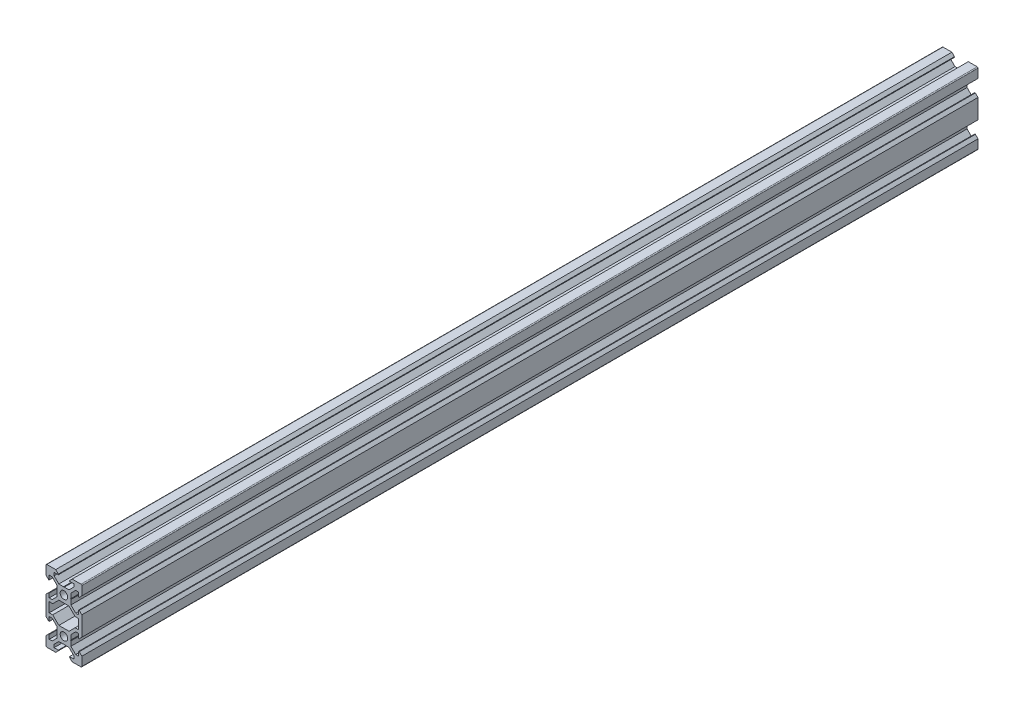
SolidWorks part; units mm, degrees
ref_plane "Front Plane" through (0, 0, 0) normal (0, 0, 1) x (1, 0, 0)
ref_plane "Top Plane" through (0, 0, 0) normal (0, 1, 0) x (1, 0, 0)
ref_plane "Right Plane" through (0, 0, 0) normal (1, 0, 0) x (0, 0, -1)
sketch "Sketch1" plane through (0, 0, 0) normal (0, 0, 1) x (1, 0, 0)
  line B0 (-8.2, -12.7) -> (-6.2393, -12.7)
  line B1 (-6.2393, -12.7) -> (-2.8393, -16.1)
  line B2 (-2.8393, -16.1) -> (2.8393, -16.1)
  line B3 (6.2393, -12.7) -> (2.8393, -16.1)
  line B4 (8.2, -12.7) -> (6.2393, -12.7)
  line B5 (8.2, -12.7) -> (8.2, -7.3)
  line B6 (8.2, -7.3) -> (6.2393, -7.3)
  line B7 (6.2393, -7.3) -> (2.8393, -3.9)
  line B8 (-2.8393, -3.9) -> (2.8393, -3.9)
  line B9 (-6.2393, -7.3) -> (-2.8393, -3.9)
  line B10 (-8.2, -7.3) -> (-6.2393, -7.3)
  line B11 (-8.2, -12.7) -> (-8.2, -7.3)
  line B12 (3.69, 0) -> (3.9, -0.21)
  line B13 (3.9, -0.21) -> (3.9, -2.8393)
  line B14 (3.9, -2.8393) -> (6.5607, -5.5)
  line B15 (6.5607, -5.5) -> (8.2, -5.5)
  line B16 (8.2, -5.5) -> (8.2, -3.125)
  line B17 (8.2, -3.125) -> (8.545, -3.125)
  line B18 (8.545, -3.125) -> (10, -4.58)
  line B19 (10, -15.42) -> (10, -4.58)
  line B20 (8.545, -16.875) -> (10, -15.42)
  line B21 (8.2, -16.875) -> (8.545, -16.875)
  line B22 (8.2, -14.5) -> (8.2, -16.875)
  line B23 (6.5607, -14.5) -> (8.2, -14.5)
  line B24 (3.9, -17.1607) -> (6.5607, -14.5)
  line B25 (3.9, -19.79) -> (3.9, -17.1607)
  line B26 (3.69, -20) -> (3.9, -19.79)
  line B27 (3.69, -20) -> (3.9, -20.21)
  line B28 (3.9, -20.21) -> (3.9, -22.8393)
  line B29 (3.9, -22.8393) -> (6.5607, -25.5)
  line B30 (6.5607, -25.5) -> (8.2, -25.5)
  line B31 (8.2, -25.5) -> (8.2, -23.125)
  line B32 (8.2, -23.125) -> (8.545, -23.125)
  line B33 (8.545, -23.125) -> (10, -24.58)
  line B34 (10, -29.5) -> (10, -24.58)
  arc B35 (9.5, -30) -> (10, -29.5) centre (9.5, -29.5) ccw
  line B36 (9.5, -30) -> (4.58, -30)
  line B37 (3.125, -28.545) -> (4.58, -30)
  line B38 (3.125, -28.2) -> (3.125, -28.545)
  line B39 (5.5, -28.2) -> (3.125, -28.2)
  line B40 (5.5, -26.5607) -> (5.5, -28.2)
  line B41 (2.8393, -23.9) -> (5.5, -26.5607)
  line B42 (0.21, -23.9) -> (2.8393, -23.9)
  line B43 (0, -23.69) -> (0.21, -23.9)
  line B44 (0, -23.69) -> (-0.21, -23.9)
  line B45 (-0.21, -23.9) -> (-2.8393, -23.9)
  line B46 (-2.8393, -23.9) -> (-5.5, -26.5607)
  line B47 (-5.5, -26.5607) -> (-5.5, -28.2)
  line B48 (-5.5, -28.2) -> (-3.125, -28.2)
  line B49 (-3.125, -28.2) -> (-3.125, -28.545)
  line B50 (-3.125, -28.545) -> (-4.58, -30)
  line B51 (-4.58, -30) -> (-9.5, -30)
  arc B52 (-10, -29.5) -> (-9.5, -30) centre (-9.5, -29.5) ccw
  line B53 (-10, -29.5) -> (-10, -24.58)
  line B54 (-8.545, -23.125) -> (-10, -24.58)
  line B55 (-8.2, -23.125) -> (-8.545, -23.125)
  line B56 (-8.2, -25.5) -> (-8.2, -23.125)
  line B57 (-6.5607, -25.5) -> (-8.2, -25.5)
  line B58 (-3.9, -22.8393) -> (-6.5607, -25.5)
  line B59 (-3.9, -20.21) -> (-3.9, -22.8393)
  line B60 (-3.69, -20) -> (-3.9, -20.21)
  line B61 (-3.69, -20) -> (-3.9, -19.79)
  line B62 (-3.9, -19.79) -> (-3.9, -17.1607)
  line B63 (-3.9, -17.1607) -> (-6.5607, -14.5)
  line B64 (-6.5607, -14.5) -> (-8.2, -14.5)
  line B65 (-8.2, -14.5) -> (-8.2, -16.875)
  line B66 (-8.2, -16.875) -> (-8.545, -16.875)
  line B67 (-8.545, -16.875) -> (-10, -15.42)
  line B68 (-10, -15.42) -> (-10, -4.58)
  line B69 (-8.545, -3.125) -> (-10, -4.58)
  line B70 (-8.2, -3.125) -> (-8.545, -3.125)
  line B71 (-8.2, -5.5) -> (-8.2, -3.125)
  line B72 (-6.5607, -5.5) -> (-8.2, -5.5)
  line B73 (-3.9, -2.8393) -> (-6.5607, -5.5)
  line B74 (-3.9, -0.21) -> (-3.9, -2.8393)
  line B75 (-3.69, 0) -> (-3.9, -0.21)
  line B76 (-3.69, 0) -> (-3.9, 0.21)
  line B77 (-3.9, 0.21) -> (-3.9, 2.8393)
  line B78 (-3.9, 2.8393) -> (-6.5607, 5.5)
  line B79 (-6.5607, 5.5) -> (-8.2, 5.5)
  line B80 (-8.2, 5.5) -> (-8.2, 3.125)
  line B81 (-8.2, 3.125) -> (-8.545, 3.125)
  line B82 (-8.545, 3.125) -> (-10, 4.58)
  line B83 (-10, 4.58) -> (-10, 9.5)
  arc B84 (-9.5, 10) -> (-10, 9.5) centre (-9.5, 9.5) ccw
  line B85 (-4.58, 10) -> (-9.5, 10)
  line B86 (-3.125, 8.545) -> (-4.58, 10)
  line B87 (-3.125, 8.2) -> (-3.125, 8.545)
  line B88 (-5.5, 8.2) -> (-3.125, 8.2)
  line B89 (-5.5, 6.5607) -> (-5.5, 8.2)
  line B90 (-2.8393, 3.9) -> (-5.5, 6.5607)
  line B91 (-0.21, 3.9) -> (-2.8393, 3.9)
  line B92 (0, 3.69) -> (-0.21, 3.9)
  line B93 (0, 3.69) -> (0.21, 3.9)
  line B94 (0.21, 3.9) -> (2.8393, 3.9)
  line B95 (2.8393, 3.9) -> (5.5, 6.5607)
  line B96 (5.5, 6.5607) -> (5.5, 8.2)
  line B97 (5.5, 8.2) -> (3.125, 8.2)
  line B98 (3.125, 8.2) -> (3.125, 8.545)
  line B99 (3.125, 8.545) -> (4.58, 10)
  line B100 (9.5, 10) -> (4.58, 10)
  arc B101 (10, 9.5) -> (9.5, 10) centre (9.5, 9.5) ccw
  line B102 (10, 4.58) -> (10, 9.5)
  line B103 (8.545, 3.125) -> (10, 4.58)
  line B104 (8.2, 3.125) -> (8.545, 3.125)
  line B105 (8.2, 5.5) -> (8.2, 3.125)
  line B106 (6.5607, 5.5) -> (8.2, 5.5)
  line B107 (3.9, 2.8393) -> (6.5607, 5.5)
  line B108 (3.9, 0.21) -> (3.9, 2.8393)
  line B109 (3.69, 0) -> (3.9, 0.21)
  circle B110 centre (0, -20) radius 2.1
  circle B111 centre (0, 0) radius 2.1
sketch_block_instance "2040 - V-Slot-1"
sketch_block "2040 - V-Slot"
extrude "Boss-Extrude1" add sketch "Sketch1" along normal blind 500
